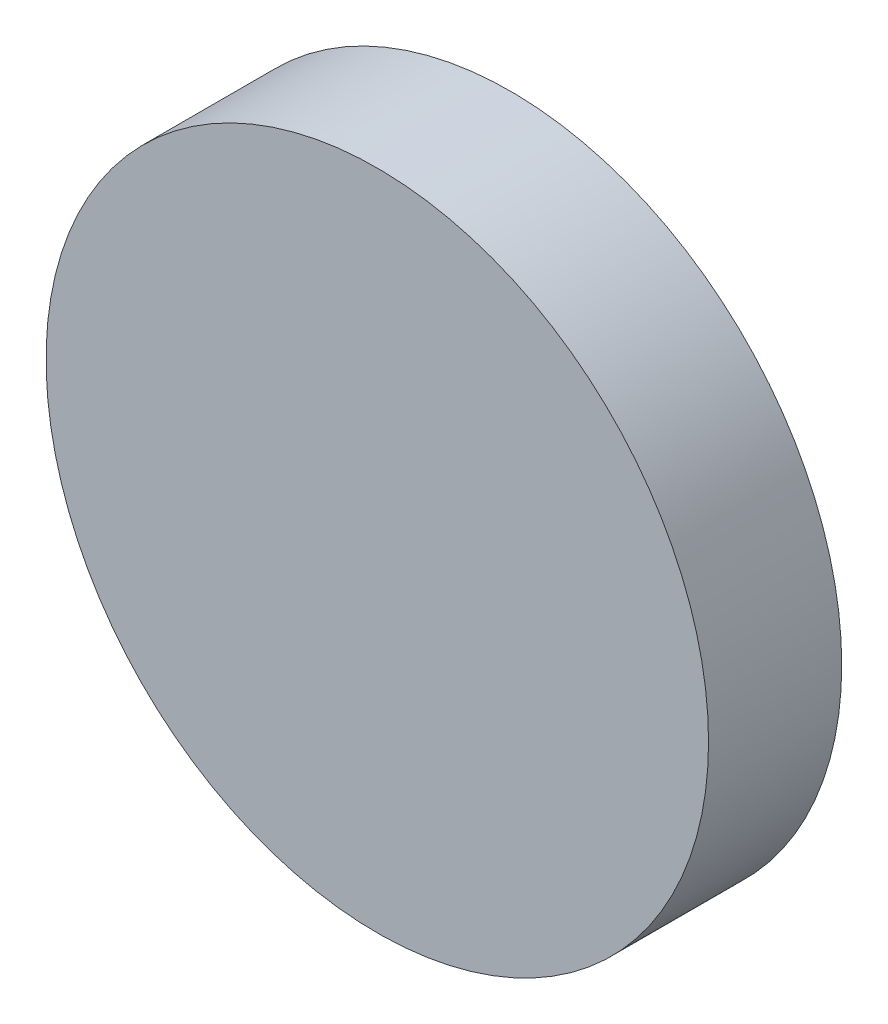
SolidWorks part; units mm, degrees
ref_plane "Front" through (0, 0, 0) normal (0, 0, 1) x (1, 0, 0)
ref_plane "Top" through (0, 0, 0) normal (0, 1, 0) x (1, 0, 0)
ref_plane "Right" through (0, 0, 0) normal (1, 0, 0) x (0, 0, -1)
sketch "Sketch1" plane through (0, 0, 0) normal (0, 0, 1) x (1, 0, 0)
  circle A0 centre (0, 0) radius 60.6425
  dimension "D1" = 121.285
extrude "Extrude1" add sketch "Sketch1" along normal blind 24.384
